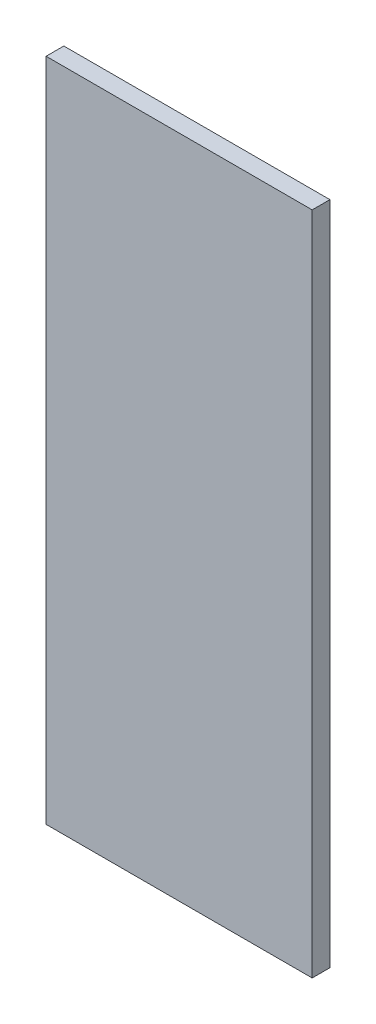
SolidWorks part; units mm, degrees
ref_plane "Front Plane" through (0, 0, 0) normal (0, 0, 1) x (1, 0, 0)
ref_plane "Top Plane" through (0, 0, 0) normal (0, 1, 0) x (1, 0, 0)
ref_plane "Right Plane" through (0, 0, 0) normal (1, 0, 0) x (0, 0, -1)
sketch "Sketch1" plane through (0, 0, 0) normal (0, 1, 0) x (1, 0, 0)
  line L0 (0, 0) -> (0, 10.16)
  line L1 (0, 10.16) -> (152.4, 10.16)
  line L2 (152.4, 10.16) -> (152.4, 0)
  line L3 (152.4, 0) -> (0, 0)
  dimension "D1" = 10.16
  dimension "D2" = 152.4
extrude "Boss-Extrude1" add sketch "Sketch1" along normal blind 381
